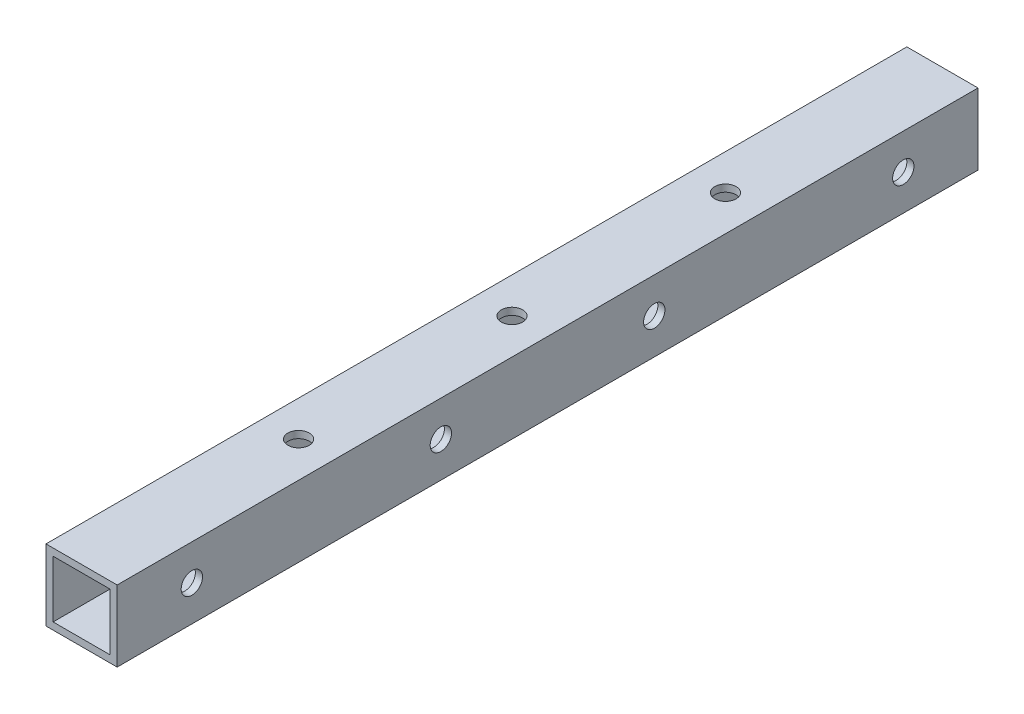
SolidWorks part; units mm, degrees
material "6063-O"
ref_plane "前视基准面" through (0, 0, 0) normal (0, 0, 1) x (1, 0, 0)
ref_plane "上视基准面" through (0, 0, 0) normal (0, 1, 0) x (1, 0, 0)
ref_plane "右视基准面" through (0, 0, 0) normal (1, 0, 0) x (0, 0, -1)
other "Configuration Table"
sketch "草图1" plane through (0, 0, 0) normal (0, 0, 1) x (1, 0, 0)
  line L1 (5, 5) -> (-5, 5)
  line L2 (5, 5) -> (5, -5)
  line L3 (5, -5) -> (-5, -5)
  line L4 (-5, 5) -> (-5, -5)
  line L5 (5, 5) -> (-5, -5) construction
  line L6 (5, -5) -> (-5, 5) construction
  point P4 (0, 0)
  dimension "D1" = 10
  dimension "D2" = 10
extrude "拉伸-薄壁1" add sketch "草图1" along normal blind 121 thin contours L1 L4 L3 L2 thin type one direction reverse wall 1
sketch "草图2" plane through (5, 0, 0) normal (1, 0, 0) x (0, 0, -1)
  line L0 (-121, 0) -> (0, 0) construction
  line L1 (-121, 5) -> (-121, -5) construction
  line L2 (0, 5) -> (0, -5) construction
  line L3 (-60.5, 0) -> (-60.5, 5) construction
  line L4 (-121, 5) -> (0, 5) construction
  circle A0 centre (-110.5, 0) radius 1.5
  circle A1 centre (-75.5, 0) radius 1.5
  circle A2 centre (-45.5, 0) radius 1.5
  circle A3 centre (-10.5, 0) radius 1.5
  dimension "D1" = 3
  dimension "D2" = 30
  dimension "D3" = 100
extrude "切除-拉伸1" cut sketch "草图2" against normal through all
sketch "草图3" plane through (0, 5, 0) normal (0, 1, 0) x (1, 0, 0)
  line L0 (5, -60.5) -> (-5, -60.5) construction
  line L1 (5, -121) -> (5, 0) construction
  line L3 (0, 0) -> (0, -121) construction
  line L4 (5, 0) -> (-5, 0) construction
  line L5 (5, -121) -> (-5, -121) construction
  circle A0 centre (0, -60.5) radius 1.5
  circle A1 centre (0, -30.5) radius 1.5
  circle A2 centre (0, -90.5) radius 1.5
  dimension "D1" = 3
  dimension "D2" = 60
extrude "切除-拉伸2" cut sketch "草图3" against normal through all
